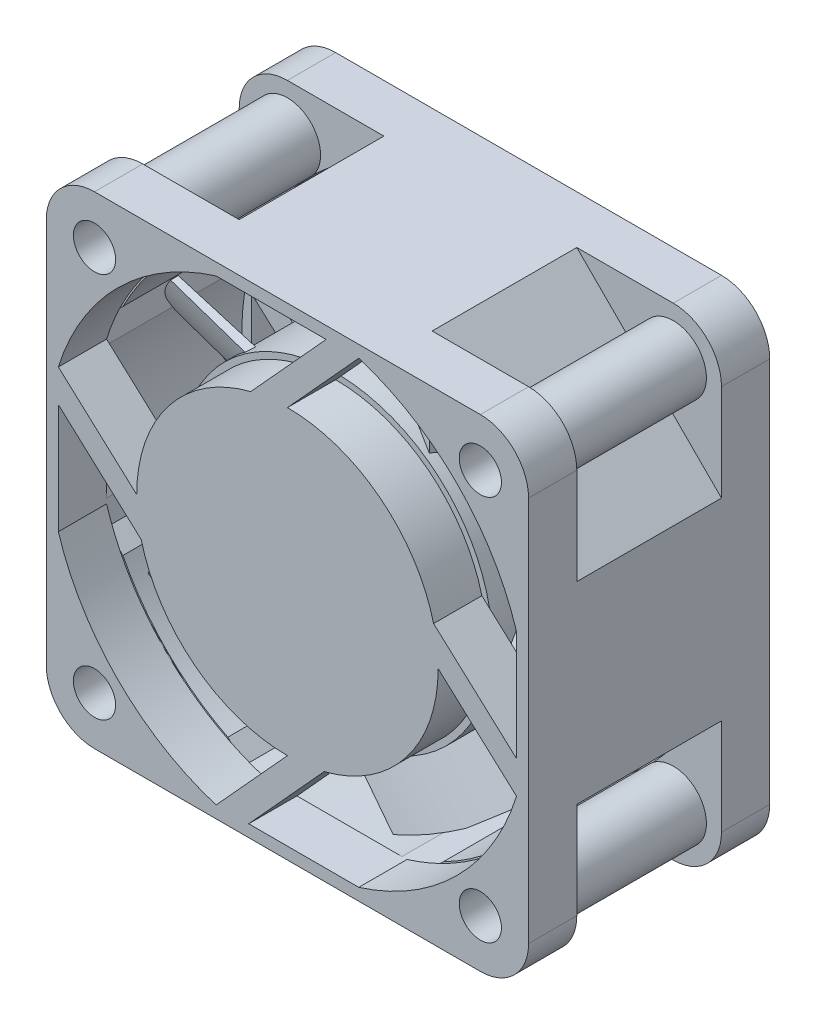
SolidWorks part; units mm, degrees
ref_plane "Front Plane" through (0, 0, 0) normal (0, 0, 1) x (1, 0, 0)
ref_plane "Top Plane" through (0, 0, 0) normal (0, 1, 0) x (1, 0, 0)
ref_plane "Right Plane" through (0, 0, 0) normal (1, 0, 0) x (0, 0, -1)
sketch "Sketch1" plane through (0, 0, 0) normal (0, 0, 1) x (1, 0, 0)
  line L0 (55, 0) -> (-55, 0) construction
  line L1 (-16, 20) -> (16, 20)
  line L2 (-20, 16) -> (-20, -16)
  line L3 (-16, -20) -> (16, -20)
  line L4 (20, 16) -> (20, -16)
  line L5 (-20, 20) -> (20, -20) construction
  line L6 (-20, -20) -> (20, 20) construction
  line L7 (0, -55) -> (0, 55) construction
  line L8 (-19, 5.9169) -> (-19, -5.9169)
  line L9 (-19, 19) -> (19, 19) construction
  line L10 (-19, 19) -> (-19, -19) construction
  line L11 (-19, -19) -> (19, -19) construction
  line L12 (19, 19) -> (19, -19) construction
  line L13 (-19, 19) -> (19, -19) construction
  line L14 (-19, -19) -> (19, 19) construction
  line L15 (-5.9169, 19) -> (5.9169, 19)
  line L16 (-5.9169, -19) -> (5.9169, -19)
  line L17 (19, 5.9169) -> (19, -5.9169)
  line L18 (-19, 0) -> (19, 0) construction
  line L19 (0, 19) -> (0, -19) construction
  line L20 (5.9169, 19) -> (0, 12.5)
  line L21 (3.2124, 19) -> (-3.048, 12.1227)
  line L22 (19, -5.9169) -> (12.5, 0)
  line L23 (19, -3.2124) -> (12.1227, 3.048)
  line L24 (19, 5.9169) -> (19, -5.9169)
  line L25 (-5.9169, -19) -> (0, -12.5)
  line L26 (-3.2124, -19) -> (3.048, -12.1227)
  line L27 (5.9169, -19) -> (-5.9169, -19)
  line L28 (-19, 5.9169) -> (-12.5, 0)
  line L29 (-19, 3.2124) -> (-12.1227, -3.048)
  line L30 (-19, -5.9169) -> (-19, 5.9169)
  arc A0 (-20, -16) -> (-16, -20) centre (-16, -16) ccw
  arc A1 (16, 20) -> (20, 16) centre (16, 16) cw
  arc A2 (-16, 20) -> (-20, 16) centre (-16, 16) ccw
  arc A3 (16, -20) -> (20, -16) centre (16, -16) ccw
  circle A4 centre (-16, 16) radius 1.75
  circle A5 centre (-16, -16) radius 1.75
  circle A6 centre (16, -16) radius 1.75
  circle A7 centre (16, 16) radius 1.75
  arc A8 (-5.9169, 19) -> (-19, 5.9169) centre (0, 0) ccw
  arc A9 (19, 5.9169) -> (5.9169, 19) centre (0, 0) ccw
  arc A10 (5.9169, -19) -> (19, -5.9169) centre (0, 0) ccw
  arc A11 (-19, -5.9169) -> (-5.9169, -19) centre (0, 0) ccw
  circle A12 centre (0, 0) radius 12.5
  circle A13 centre (0, 0) radius 12.5
  circle A14 centre (0, 0) radius 12.5
  circle A15 centre (0, 0) radius 12.5
  point P0 (0, 0)
  point P26 (0, 0)
  point P69 (0, 0)
  dimension "D2" = 4
  dimension "D3" = 3.5
  dimension "D5" = 19.9
  dimension "D6" = 25
  dimension "D1" = 40
  dimension "D4" = 38
  dimension "D7" = 2
  dimension "D8" = 4
extrude "Boss-Extrude1" add sketch "Sketch1" along normal blind 4 contours L3 A3 L4 A1 L1 A2 L2 A0 A11 L8 A8 L15 A9 L17 A10 L16 A5 A4 A6 A7 | A12 | A12 L20 L15 L21 | A12 L22 L17 L23 | A12 L25 L16 L26 | A12 L28 L8 L29
sketch "Sketch2" plane through (0, 0, 4) normal (0, 0, 1) x (1, 0, 0)
  line L0 (20, 16) -> (20, -16) construction
  line L1 (-8, 20) -> (8, 20)
  line L2 (-20, 8) -> (-20, -8)
  line L3 (-8, -20) -> (8, -20)
  line L4 (20, 8) -> (20, -8)
  line L5 (-20, 20) -> (20, -20) construction
  line L6 (-20, -20) -> (20, 20) construction
  line L7 (-16, -20) -> (16, -20) construction
  line L8 (8, 20) -> (20, 8)
  line L9 (-20, 8) -> (-8, 20)
  line L10 (-20, -8) -> (-8, -20)
  line L11 (8, -20) -> (20, -8)
  line L12 (-19, 7.5858) -> (-7.5858, 19)
  line L13 (-7.5858, 19) -> (7.5858, 19)
  line L14 (7.5858, 19) -> (19, 7.5858)
  line L15 (19, 7.5858) -> (19, -7.5858)
  line L16 (7.5858, -19) -> (19, -7.5858)
  line L17 (-7.5858, -19) -> (7.5858, -19)
  line L18 (-19, -7.5858) -> (-7.5858, -19)
  line L19 (-19, 7.5858) -> (-19, -7.5858)
  point P0 (0, 0)
  dimension "D2" = 1
extrude "Boss-Extrude2" add sketch "Sketch2" along normal blind 12
sketch "Sketch3" plane through (0, 0, 4) normal (0, 0, 1) x (1, 0, 0)
  circle A0 centre (0, 0) radius 13
  dimension "D1" = 26
extrude "Boss-Extrude3" add sketch "Sketch3" along normal blind 12
ref_plane "Plane1" through (0, 18.5, 0) normal (0, 1, 0) x (1, 0, 0)
ref_plane "Plane2" through (0, 10.5, 0) normal (0, 1, 0) x (1, 0, 0)
sketch "Sketch5" plane through (0, 18.5, 0) normal (0, 1, 0) x (1, 0, 0)
  line L0 (-7.5834, -5) -> (-7.7848, -5.4577)
  line L1 (7.4662, -15) -> (7.2982, -15.471)
  spline S0 degree 3 poles (7.2982, -15.471) (0.7604, -13.1396) (-2.7167, -7.6876) (-7.7848, -5.4577) knots 0 0 0 0 1 1 1 1
  spline S1 degree 1 poles (7.4662, -15) (-7.5834, -5) knots 0 0 1 1 construction
  spline S2 degree 3 poles (7.4662, -15) (7.0748, -14.8604) (6.2943, -14.5501) (4.8371, -13.8534) (3.1439, -12.8438) (1.2769, -11.4837) (-1.0704, -9.5633) (-3.8661, -7.1437) (-6.2708, -5.5775) (-7.5834, -5) knots 0 0 0 0 0.0625 0.125 0.25 0.375 0.5 0.75 1 1 1 1
  dimension "D4" = 20.8232
  dimension "D5" = 18.1969
  dimension "D7" = 16.6108
  dimension "D2" = 5
  dimension "D3" = 15
  dimension "D6" = 7.4662
  dimension "D1" = 0.5
sketch "Sketch6" plane through (0, 10.5, 0) normal (0, 1, 0) x (1, 0, 0)
  line L0 (7.4662, -15) -> (7.2982, -15.471) construction
  line L1 (-7.5834, -5) -> (-7.7848, -5.4577) construction
  line L2 (7.4662, -15) -> (7.2982, -15.471) construction
  line L3 (-7.5834, -5) -> (-7.7848, -5.4577) construction
  line L4 (-7.6347, -4.8682) -> (-7.9166, -5.5089)
  line L5 (7.5939, -14.9394) -> (7.3588, -15.5987)
  spline S0 degree 3 poles (-1706.7106, 1014.4644) (85.5054, -4.3964) (25.7057, -23.831) (4.8371, -13.8534) (3.1439, -12.8438) (1.2769, -11.4837) (-1.0704, -9.5633) (-29.6254, 15.1516) (-83.9873, -18.5303) (-1106.5051, -1675.2142) knots -3.330381 -3.330381 -3.330381 -3.330381 0.0625 0.125 0.25 0.375 0.5 0.75 6.758865 6.758865 6.758865 6.758865 only from (7.4662, -15) to (-7.5834, -5) construction
  spline S1 degree 3 poles (1327.9479, 1484.5372) (-1176.3596, -1633.3308) (1134.549, 1645.529) (-1214.8824, -1599.507) knots -5.78387 -5.78387 -5.78387 -5.78387 6.892651 6.892651 6.892651 6.892651 only from (7.2982, -15.471) to (-7.7848, -5.4577) construction
  spline S2 degree 3 poles (7.4662, -15) (7.0748, -14.8604) (6.2943, -14.5501) (4.8371, -13.8534) (3.1439, -12.8438) (1.2769, -11.4837) (-1.0704, -9.5633) (-3.8661, -7.1437) (-6.2708, -5.5775) (-7.5834, -5) knots 0 0 0 0 0.0625 0.125 0.25 0.375 0.5 0.75 1 1 1 1 construction
  spline S3 degree 3 poles (7.2982, -15.471) (0.7604, -13.1396) (-2.7167, -7.6876) (-7.7848, -5.4577) knots 0 0 0 0 1 1 1 1 construction
  spline S4 degree 1 poles (7.3588, -15.5987) (-7.9166, -5.5089) knots 0 0 1 1 construction
  spline S5 degree 1 poles (7.5939, -14.9394) (-7.6347, -4.8682) knots 0 0 1 1 construction
  spline S6 degree 3 poles (7.3588, -15.5987) (6.9493, -15.4527) (6.1297, -15.1348) (4.6054, -14.4115) (2.8429, -13.3665) (0.9174, -11.9652) (-1.4776, -10.0054) (-4.2927, -7.5662) (-6.6333, -6.0735) (-7.9166, -5.5089) knots -0.004802 -0.004802 -0.004802 -0.004802 0.058374 0.12155 0.247903 0.374256 0.500609 0.753315 1.00602 1.00602 1.00602 1.00602
  spline S7 degree 3 poles (-7.6347, -4.8682) (-6.3013, -5.4549) (-3.8409, -7.0257) (-1.0174, -9.4785) (1.3519, -11.4158) (3.2348, -12.7852) (4.9415, -13.7964) (6.4125, -14.4938) (7.2001, -14.799) (7.5939, -14.9394) knots -0.005014 -0.005014 -0.005014 -0.005014 0.247693 0.500399 0.626752 0.753105 0.879458 0.942635 1.005811 1.005811 1.005811 1.005811
  dimension "D1" = 0.1
loft "Loft1" add profiles "Sketch6", "Sketch5"
pattern_circular "CirPattern8" count 5 over 360 about axis through (0, 0, 16) along (0, 0, 1) of "Loft1"
ref_plane "Plane3" through (0, 0, 10) normal (0, 0, -1) x (-1, 0, 0)
mirror "Mirror1" about plane through (0, 0, 10) normal (0, 0, -1) of "Boss-Extrude1"
sketch "Sketch9" plane through (0, 0, 16) normal (0, 0, -1) x (-1, 0, 0)
  circle A0 centre (0, 0) radius 19.9 construction
  circle A1 centre (0, 0) radius 18.78
  arc A2 (19, 5.9169) -> (5.9169, 19) centre (0, 0) ccw construction
  circle A3 centre (0, 0) radius 19.78
  dimension "D1" = 1
  dimension "D2" = 0.12
extrude "Cut-Extrude1" cut sketch "Sketch9" along normal blind 12
sketch "Sketch10" plane through (0, 0, 16) normal (0, 0, -1) x (-1, 0, 0)
  circle A0 centre (-16, 16) radius 1.75 construction
  circle A1 centre (-16, 16) radius 1.75
  circle A2 centre (-16, 16) radius 2.75
  circle A3 centre (16, 16) radius 1.75
  circle A4 centre (16, 16) radius 2.75
  circle A5 centre (16, -16) radius 1.75
  circle A6 centre (16, -16) radius 2.75
  circle A7 centre (-16, -16) radius 1.75
  circle A8 centre (-16, -16) radius 2.75
  point P20 (0, 0)
  dimension "D1" = 1
  dimension "D2" = 4
extrude "Boss-Extrude4" add sketch "Sketch10" along normal blind 12
